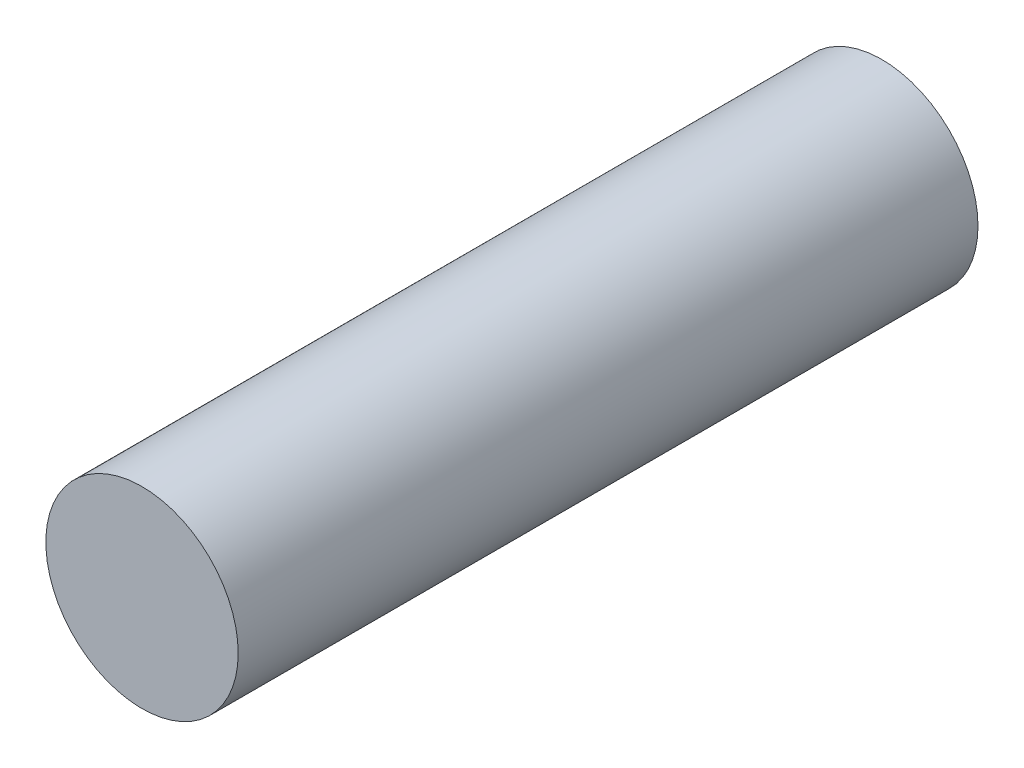
SolidWorks part; units mm, degrees
material "PA Type 6"
ref_plane "Front Plane" through (0, 0, 0) normal (0, 0, 1) x (1, 0, 0)
ref_plane "Top Plane" through (0, 0, 0) normal (0, 1, 0) x (1, 0, 0)
ref_plane "Right Plane" through (0, 0, 0) normal (1, 0, 0) x (0, 0, -1)
sketch "Sketch1" plane through (0, 0, 0) normal (0, 0, 1) x (1, 0, 0)
  circle A0 centre (0, 0) radius 6.5
  dimension "D1" = 13
extrude "Boss-Extrude1" add sketch "Sketch1" along normal mid plane 50
